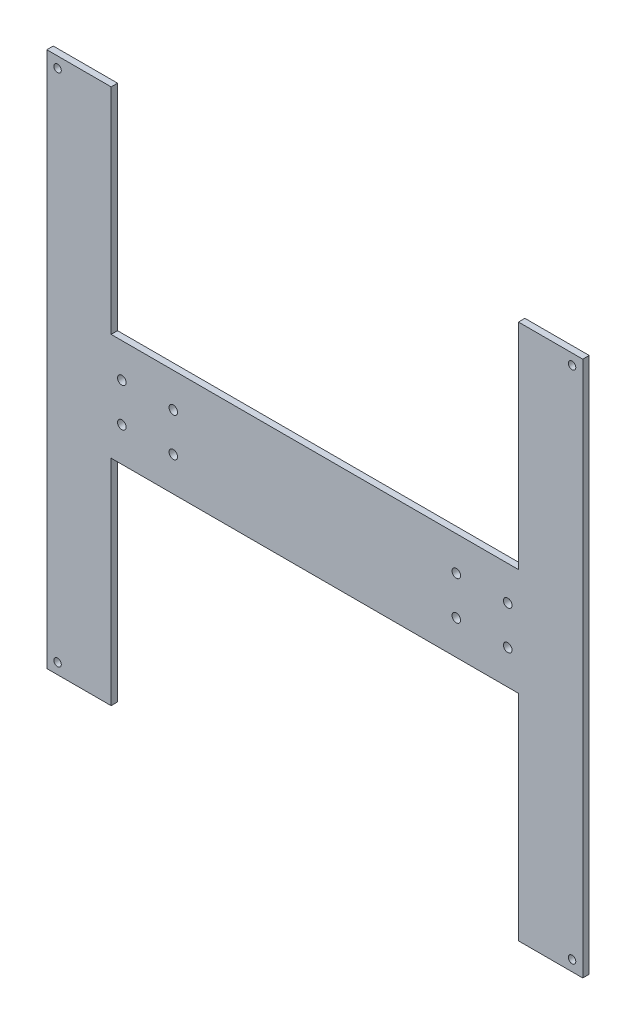
SolidWorks part; units mm, degrees
ref_plane "Front Plane" through (0, 0, 0) normal (0, 0, 1) x (1, 0, 0)
ref_plane "Top Plane" through (0, 0, 0) normal (0, 1, 0) x (1, 0, 0)
ref_plane "Right Plane" through (0, 0, 0) normal (1, 0, 0) x (0, 0, -1)
sketch "Sketch1" plane through (0, 0, 0) normal (0, 0, 1) x (1, 0, 0)
  line L0 (95, 125) -> (125, 125)
  line L1 (-125, 125) -> (-95, 125)
  line L2 (-125, 125) -> (-125, -125)
  line L3 (-125, -125) -> (-95, -125)
  line L4 (125, 125) -> (125, -125)
  line L5 (0, 0) -> (-125, 0) construction
  line L6 (-95, -25) -> (95, -25)
  line L7 (-95, -125) -> (-95, -25)
  line L8 (-95, 125) -> (-95, 25)
  line L9 (-95, 25) -> (95, 25)
  line L10 (95, 125) -> (95, 25)
  line L11 (95, -125) -> (95, -25)
  line L12 (95, -125) -> (125, -125)
  line L13 (0, 0) -> (0, 25) construction
  circle A0 centre (90, 9) radius 2
  circle A1 centre (90, -9) radius 2
  circle A2 centre (66, 9) radius 2
  circle A3 centre (66, -9) radius 2
  circle A4 centre (-66, -9) radius 2
  circle A5 centre (-66, 9) radius 2
  circle A6 centre (-90, -9) radius 2
  circle A7 centre (-90, 9) radius 2
  point P0 (0, 0)
  point P6 (0, 75)
  dimension "D1" = 250
  dimension "D2" = 250
  dimension "D3" = 100
  dimension "D4" = 190
extrude "Boss-Extrude1" add sketch "Sketch1" along normal blind 3
sketch "Sketch3" plane through (0, 0, 3) normal (0, 0, 1) x (1, 0, 0)
  circle A0 centre (-120, 120) radius 1.75
  circle A1 centre (120, 120) radius 1.75
  circle A2 centre (-120, -120) radius 1.75
  circle A3 centre (120, -120) radius 1.75
extrude "Cut-Extrude1" cut sketch "Sketch3" against normal blind 3
